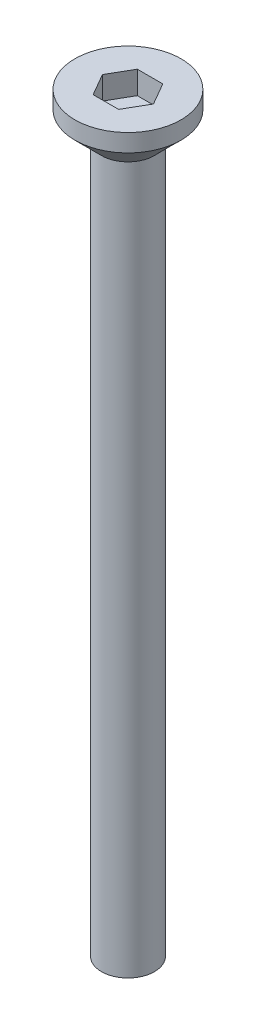
SolidWorks part; units mm, degrees
material "AISI 304"
ref_plane "前视基准面" through (0, 0, 0) normal (0, 0, 1) x (1, 0, 0)
ref_plane "上视基准面" through (0, 0, 0) normal (0, 1, 0) x (1, 0, 0)
ref_plane "右视基准面" through (0, 0, 0) normal (1, 0, 0) x (0, 0, -1)
sketch "草图1" plane through (0, 0, 0) normal (0, 1, 0) x (1, 0, 0)
  circle A0 centre (0, 0) radius 3
  dimension "D1" = 6
extrude "沉头头" add sketch "草图1" along normal blind 2.5
chamfer "倒角1" distance 1.5 angle 45 1 edges at (0, 0, 3)
sketch "草图2" plane through (0, 2.5, 0) normal (0, 1, 0) x (1, 0, 0)
  line L1 (1.4434, 0) -> (0.7217, 1.25)
  line L2 (0.7217, 1.25) -> (-0.7217, 1.25)
  line L3 (-0.7217, 1.25) -> (-1.4434, 0)
  line L4 (-1.4434, 0) -> (-0.7217, -1.25)
  line L5 (-0.7217, -1.25) -> (0.7217, -1.25)
  line L6 (0.7217, -1.25) -> (1.4434, 0)
  circle A0 centre (0, 0) radius 1.25 construction
  dimension "D1" = 2.5
extrude "内六角口" cut sketch "草图2" against normal blind 1.3
sketch "草图3" plane through (0, 0, 0) normal (0, -1, 0) x (1, 0, 0)
  circle A0 centre (0, 0) radius 1.5
  dimension "D1" = 3
extrude "螺纹长" add sketch "草图3" along normal blind 40
